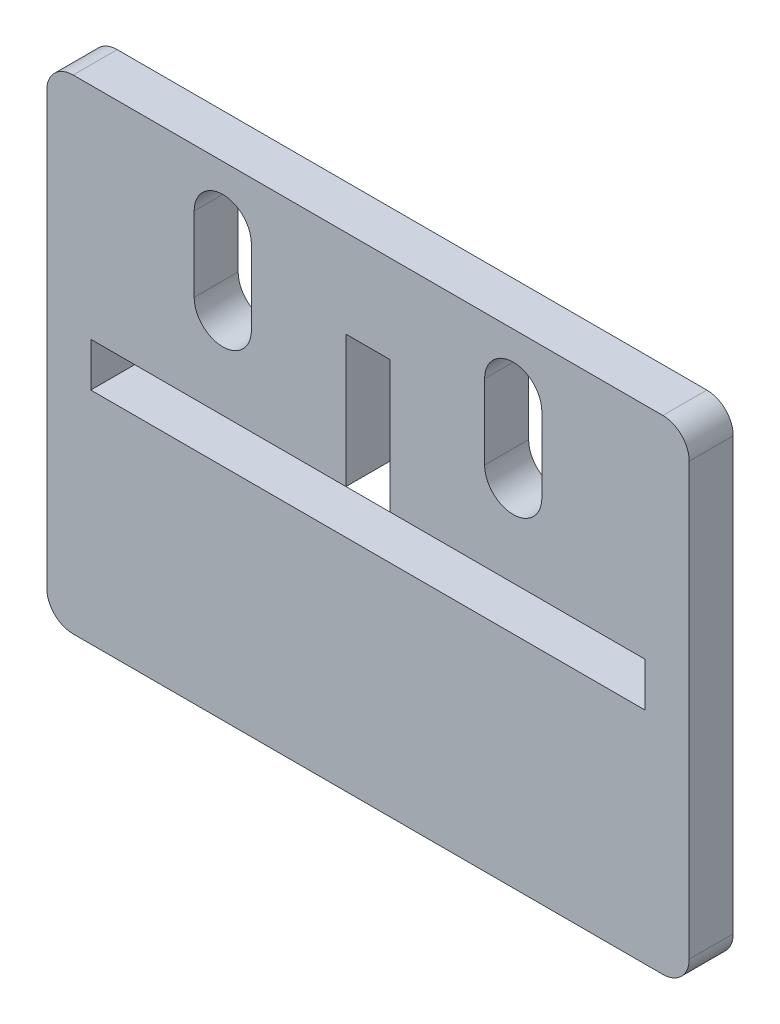
SolidWorks part; units mm, degrees
ref_plane "前视基准面" through (0, 0, 0) normal (0, 0, 1) x (1, 0, 0)
ref_plane "上视基准面" through (0, 0, 0) normal (0, 1, 0) x (1, 0, 0)
ref_plane "右视基准面" through (0, 0, 0) normal (1, 0, 0) x (0, 0, -1)
sketch "草图1" plane through (0, 0, 0) normal (0, 0, 1) x (1, 0, 0)
  line L0 (31.5, 2.5) -> (-31.5, 2.5) construction
  line L1 (33.5, -27.5) -> (-33.5, -27.5)
  line L2 (36.5, -24.5) -> (36.5, 24.5)
  line L3 (33.5, 27.5) -> (-33.5, 27.5)
  line L4 (-36.5, -24.5) -> (-36.5, 24.5)
  line L5 (0, 27.5) -> (0, -27.5) construction
  line L6 (36.5, 0) -> (-36.5, 0) construction
  line L7 (31.5, -2.5) -> (-31.5, -2.5) construction
  line L8 (-31.5, 2.5) -> (-31.5, -2.5)
  line L9 (-31.5, -2.5) -> (31.5, -2.5)
  line L10 (31.5, -2.5) -> (31.5, 2.5)
  line L11 (31.5, 2.5) -> (-31.5, 2.5) construction
  line L12 (-31.5, 2.5) -> (-2.5, 2.5)
  line L13 (2.5, 17.5) -> (-2.5, 17.5)
  line L14 (2.5, 17.5) -> (2.5, 2.5)
  line L15 (2.5, 2.5) -> (-2.5, 2.5) construction
  line L16 (-2.5, 17.5) -> (-2.5, 2.5)
  line L17 (0, 2.5) -> (0, 17.5) construction
  line L18 (2.5, 10) -> (-2.5, 10) construction
  line L19 (2.5, 2.5) -> (31.5, 2.5)
  line L20 (13.25, 21) -> (13.25, 12.5) construction
  line L21 (19.75, 12.5) -> (19.75, 21) construction
  line L22 (13.25, 21) -> (13.25, 12.5)
  line L23 (19.75, 12.5) -> (19.75, 21)
  line L24 (-13.25, 21) -> (-13.25, 12.5)
  line L25 (-19.75, 12.5) -> (-19.75, 21)
  arc A0 (36.5, 24.5) -> (33.5, 27.5) centre (33.5, 24.5) ccw
  arc A1 (33.5, -27.5) -> (36.5, -24.5) centre (33.5, -24.5) ccw
  arc A2 (-33.5, -27.5) -> (-36.5, -24.5) centre (-33.5, -24.5) cw
  arc A3 (-33.5, 27.5) -> (-36.5, 24.5) centre (-33.5, 24.5) ccw
  arc A4 (13.25, 12.5) -> (19.75, 12.5) centre (16.5, 12.5) ccw construction
  arc A5 (19.75, 21) -> (13.25, 21) centre (16.5, 21) ccw construction
  arc A6 (13.25, 12.5) -> (19.75, 12.5) centre (16.5, 12.5) ccw
  arc A7 (19.75, 21) -> (13.25, 21) centre (16.5, 21) ccw
  arc A8 (-19.75, 21) -> (-13.25, 21) centre (-16.5, 21) cw
  arc A9 (-13.25, 12.5) -> (-19.75, 12.5) centre (-16.5, 12.5) cw
  point P0 (0, 0)
  point P7 (0, 2.5)
  point P12 (0, 10)
  point P18 (36.5, 27.5)
  point P24 (36.5, -27.5)
  point P29 (-36.5, 27.5)
  dimension "D7" = 3
  dimension "D1" = 73
  dimension "D2" = 55
  dimension "D3" = 63
  dimension "D4" = 2.5
  dimension "D5" = 5
  dimension "D6" = 15
extrude "凸台-拉伸1" add sketch "草图1" along normal blind 5
